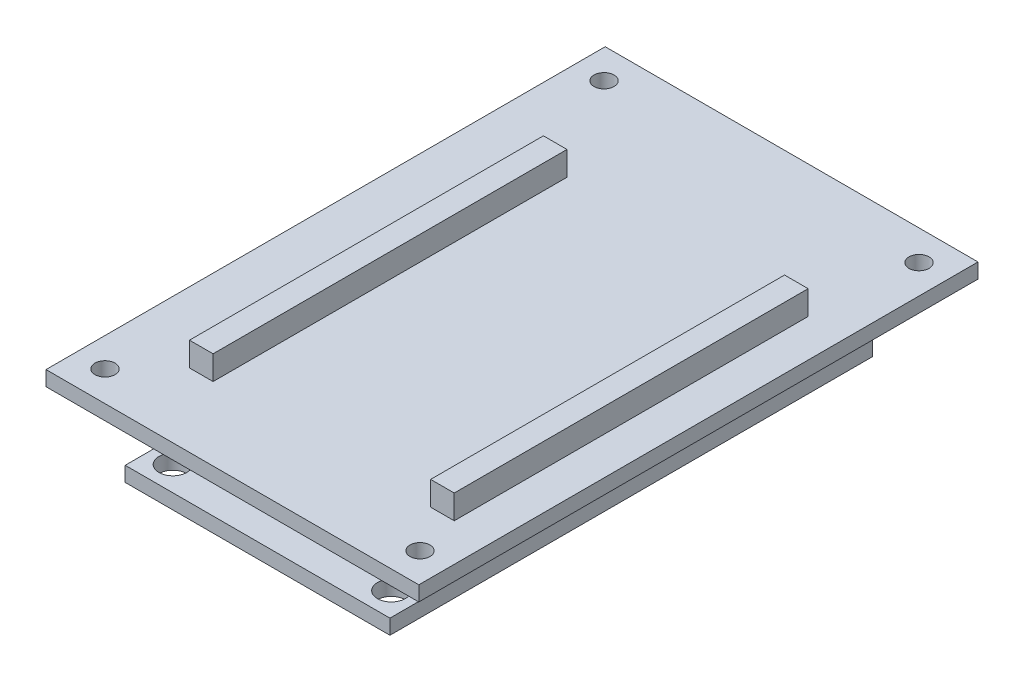
SolidWorks part; units mm, degrees
ref_plane "Front Plane" through (0, 0, 0) normal (0, 0, 1) x (1, 0, 0)
ref_plane "Top Plane" through (0, 0, 0) normal (0, 1, 0) x (1, 0, 0)
ref_plane "Right Plane" through (0, 0, 0) normal (1, 0, 0) x (0, 0, -1)
sketch "Sketch1" plane through (0, 0, 0) normal (0, 1, 0) x (1, 0, 0)
  line L0 (14.2494, -25.9715) -> (-14.2494, 25.9715) construction
  line L1 (-14.2494, 25.9715) -> (14.2494, 25.9715)
  line L2 (-14.2494, 25.9715) -> (-14.2494, -25.9715)
  line L3 (-14.2494, -25.9715) -> (14.2494, -25.9715)
  line L4 (14.2494, 25.9715) -> (14.2494, -25.9715)
  line L5 (-11.7602, -23.3299) -> (11.7602, 23.3299) construction
  line L6 (-11.7602, 23.3299) -> (11.7602, 23.3299) construction
  line L7 (-11.7602, 23.3299) -> (-11.7602, -23.3299) construction
  line L8 (-11.7602, -23.3299) -> (11.7602, -23.3299) construction
  line L9 (11.7602, 23.3299) -> (11.7602, -23.3299) construction
  circle A0 centre (-11.7602, 23.3299) radius 1.4986
  circle A1 centre (11.7602, -23.3299) radius 1.4986
  circle A2 centre (-11.7602, -23.3299) radius 1.4986
  circle A3 centre (11.7602, 23.3299) radius 1.4986
  point P12 (0, 0)
  point P13 (12.5412, -25.9715)
  point P15 (1.0707, 16.9876)
  point P17 (11.995, 24.5411)
  point P18 (-4.3548, 16.5897)
  point P19 (0, 0)
  point P20 (-12.5412, -25.006)
  dimension "D3" = 2.9972
  dimension "D1" = 28.4988
  dimension "D2" = 51.943
  dimension "D4" = 23.5204
  dimension "D5" = 46.6598
extrude "Boss-Extrude1" add sketch "Sketch1" along normal blind 1.6002
sketch "Sketch2" plane through (0, 1.6002, 0) normal (0, 1, 0) x (1, 0, 0)
  line L0 (-14.2494, 25.9715) -> (-14.2494, -25.9715) construction
  line L1 (-14.2494, -19.05) -> (-11.7094, -19.05)
  line L2 (-14.2494, -19.05) -> (-14.2494, 19.05)
  line L3 (-14.2494, 19.05) -> (-11.7094, 19.05)
  line L4 (-11.7094, -19.05) -> (-11.7094, 19.05)
  line L5 (14.2494, -25.9715) -> (14.2494, 25.9715) construction
  line L6 (14.2494, -19.05) -> (11.7094, -19.05)
  line L7 (14.2494, -19.05) -> (14.2494, 19.05)
  line L8 (14.2494, 19.05) -> (11.7094, 19.05)
  line L9 (11.7094, -19.05) -> (11.7094, 19.05)
  line L10 (-11.7094, 19.05) -> (11.7094, -19.05) construction
  line L11 (-11.7094, 19.05) -> (11.7094, 19.05) construction
  line L12 (-11.7094, -19.05) -> (11.7094, -19.05) construction
  dimension "D1" = 38.1
  dimension "D2" = 2.54
extrude "Boss-Extrude2" add sketch "Sketch2" along normal blind 8.2042
sketch "Sketch3" plane through (0, 0, 0) normal (0, -1, 0) x (1, 0, 0)
  line L0 (7.874, 18.3515) -> (-7.874, 0.5715) construction
  line L1 (-7.874, 18.3515) -> (7.874, 18.3515)
  line L2 (-7.874, 18.3515) -> (-7.874, 0.5715)
  line L3 (-7.874, 0.5715) -> (7.874, 0.5715)
  line L4 (7.874, 18.3515) -> (7.874, 0.5715)
  line L5 (0, 9.4615) -> (0, 0) construction
  line L6 (-14.2494, 25.9715) -> (14.2494, 25.9715) construction
  dimension "D1" = 17.78
  dimension "D2" = 15.748
  dimension "D3" = 7.62
extrude "Boss-Extrude3" add sketch "Sketch3" along normal offset from surface (3.2258 mm away) 4.826 up to face at (-11.7602, 1.6002, 24.8285)
ref_plane "Plane1" through (0, 5.6134, 0) normal (0, 1, 0) x (1, 0, 0)
sketch "Sketch4" plane through (0, 5.6134, 0) normal (0, 1, 0) x (1, 0, 0)
  line L0 (18.3096, 33.274) -> (-21.8224, -26.924) construction
  line L1 (-21.8224, 33.274) -> (18.3096, 33.274)
  line L2 (-21.8224, 33.274) -> (-21.8224, -26.924)
  line L3 (-21.8224, -26.924) -> (18.3096, -26.924)
  line L4 (18.3096, 33.274) -> (18.3096, -26.924)
  line L5 (15.1981, -23.6855) -> (-18.7109, 30.0355) construction
  line L6 (-18.7109, 30.0355) -> (15.1981, 30.0355) construction
  line L7 (-18.7109, 30.0355) -> (-18.7109, -23.6855) construction
  line L8 (-18.7109, -23.6855) -> (15.1981, -23.6855) construction
  line L9 (15.1981, 30.0355) -> (15.1981, -23.6855) construction
  circle A0 centre (-18.7109, 30.0355) radius 1.0795
  circle A2 centre (15.1981, 30.0355) radius 1.0795
  circle A3 centre (15.1981, -23.6855) radius 1.0795
  circle A4 centre (-18.7109, -23.6855) radius 1.0795
  point P4 (-1.7564, 3.175)
  point P10 (-1.7564, 3.175)
  point P14 (16.6985, 30.2661)
  point P16 (16.3376, -24.1303)
  point P18 (-19.7591, -23.9161)
  dimension "D5" = 2.159
  dimension "D1" = 60.198
  dimension "D2" = 40.132
  dimension "D3" = 3.175
  dimension "D4" = 1.7564
  dimension "D6" = 33.909
  dimension "D7" = 53.721
extrude "Boss-Extrude4" add sketch "Sketch4" along normal blind 1.6002
equation "\"D4@Sketch1\"=1.044-\"D3@Sketch1\""
equation "\"D5@Sketch1\"=1.955-\"D3@Sketch1\""
